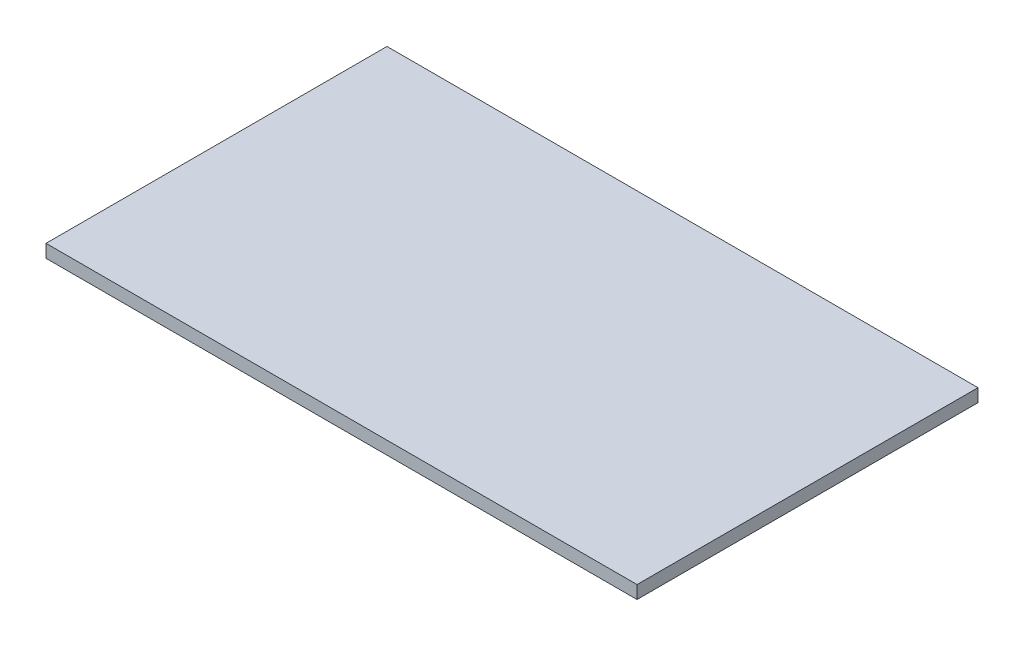
SolidWorks part; units mm, degrees
ref_plane "Front Plane" through (0, 0, 0) normal (0, 0, 1) x (1, 0, 0)
ref_plane "Top Plane" through (0, 0, 0) normal (0, 1, 0) x (1, 0, 0)
ref_plane "Right Plane" through (0, 0, 0) normal (1, 0, 0) x (0, 0, -1)
sketch "Sketch1" plane through (0, 0, 0) normal (0, 1, 0) x (1, 0, 0)
  line L1 (0, 0) -> (260, 0)
  line L2 (0, 0) -> (0, 150)
  line L3 (0, 150) -> (260, 150)
  line L4 (260, 0) -> (260, 150)
  dimension "D1" = 150
  dimension "D2" = 260
extrude "Boss-Extrude1" add sketch "Sketch1" along normal blind 5.715
